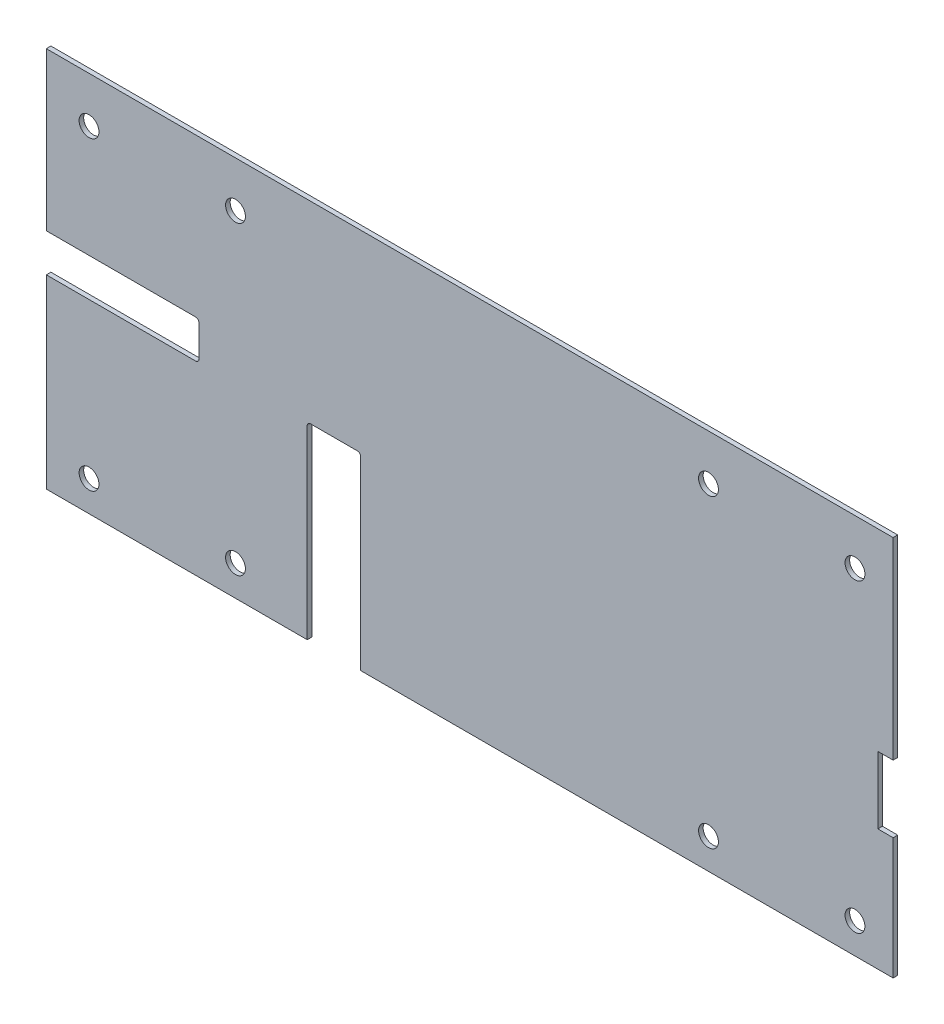
SolidWorks part; units mm, degrees
ref_plane "Plan de face" through (0, 0, 0) normal (0, 0, 1) x (1, 0, 0)
ref_plane "Plan de dessus" through (0, 0, 0) normal (0, 1, 0) x (1, 0, 0)
ref_plane "Plan de droite" through (0, 0, 0) normal (1, 0, 0) x (0, 0, -1)
sketch "Esquisse1" plane through (0, 0, 0) normal (0, 0, 1) x (1, 0, 0)
  line L1 (277.5, -125) -> (-277.5, -125)
  line L2 (277.5, -125) -> (277.5, 125)
  line L3 (277.5, 125) -> (-277.5, 125)
  line L4 (-277.5, -125) -> (-277.5, 125)
  line L5 (277.5, -125) -> (-277.5, 125) construction
  line L6 (277.5, 125) -> (-277.5, -125) construction
  line L7 (-249.5, 95) -> (-153.5, 95) construction
  line L8 (-249.5, 95) -> (-249.5, -105) construction
  line L9 (-249.5, -105) -> (-153.5, -105) construction
  line L10 (-153.5, 95) -> (-153.5, -105) construction
  line L11 (156.5, 95) -> (252.5, 95) construction
  line L12 (156.5, 95) -> (156.5, -105) construction
  line L13 (156.5, -105) -> (252.5, -105) construction
  line L14 (252.5, 95) -> (252.5, -105) construction
  circle A0 centre (156.5, 95) radius 6.5
  circle A1 centre (252.5, 95) radius 6.5
  circle A2 centre (156.5, -105) radius 6.5
  circle A3 centre (252.5, -105) radius 6.5
  circle A4 centre (-153.5, -105) radius 6.5
  circle A5 centre (-153.5, 95) radius 6.5
  circle A6 centre (-249.5, 95) radius 6.5
  circle A7 centre (-249.5, -105) radius 6.5
  point P0 (0, 0)
  dimension "D11" = 13
  dimension "D1" = 555
  dimension "D2" = 250
  dimension "D3" = 96
  dimension "D4" = 96
  dimension "D5" = 200
  dimension "D6" = 20
  dimension "D7" = 0
  dimension "D8" = 502
  dimension "D9" = 25
  dimension "D10" = 0
extrude "Boss.-Extru.1" add sketch "Esquisse1" along normal blind 3
sketch "Esquisse2" plane through (0, 0, 3) normal (0, 0, 1) x (1, 0, 0)
  line L0 (277.5, 125) -> (-277.5, 125) construction
  line L1 (-277.5, 125) -> (-177.5, 125)
  line L2 (-277.5, 125) -> (-277.5, 122)
  line L3 (-277.5, 122) -> (-177.5, 122)
  line L4 (-177.5, 125) -> (-177.5, 122)
  line L5 (-100, 125) -> (100, 125)
  line L6 (-100, 125) -> (-100, 122)
  line L7 (-100, 122) -> (100, 122)
  line L8 (100, 125) -> (100, 122)
  line L9 (277.5, -125) -> (277.5, 125) construction
  line L10 (277.5, 125) -> (177.545, 125)
  line L12 (274.5, 122) -> (177.545, 122)
  line L13 (177.545, 125) -> (177.545, 122)
  line L14 (277.5, -125) -> (274.5, -125)
  line L15 (277.5, -125) -> (277.5, -50)
  line L16 (277.5, -50) -> (274.5, -50)
  line L17 (274.5, -125) -> (274.5, -50)
  line L18 (277.5, 40) -> (274.5, 40)
  line L19 (277.5, 40) -> (277.5, 125)
  line L21 (274.5, 40) -> (274.5, 122)
  point P16 (0, 122)
  dimension "D1" = 100
  dimension "D2" = 100
  dimension "D3" = 3
  dimension "D4" = 0
  dimension "D5" = 200
  dimension "D6" = 3
  dimension "D7" = 75
  dimension "D8" = 85
extrude "Enlèv. mat.-Extru.1" [suppressed] cut sketch "Esquisse2" against normal blind 10
sketch "Esquisse3" [suppressed] plane through (0, 0, 3) normal (0, 0, 1) x (1, 0, 0)
  line L0 (274.5, 122) -> (274.5, 40) construction
  line L1 (-75.5, 122) -> (-72.5, 122)
  line L2 (-75.5, 122) -> (-75.5, 40)
  line L3 (-75.5, 40) -> (-72.5, 40)
  line L4 (-72.5, 122) -> (-72.5, 40)
  line L5 (-100, 122) -> (100, 122) construction
  line L7 (-277.5, -125) -> (274.5, -125) construction
  line L8 (-75.5, -125) -> (-72.5, -125)
  line L9 (-75.5, -125) -> (-75.5, -50)
  line L10 (-75.5, -50) -> (-72.5, -50)
  line L11 (-72.5, -125) -> (-72.5, -50)
  dimension "D1" = 3
  dimension "D2" = 350
  dimension "D3" = 0
  dimension "D4" = 82
  dimension "D5" = 75
  dimension "D6" = 0
extrude "Enlèv. mat.-Extru.2" [suppressed] cut sketch "Esquisse3" against normal blind 3
mirror "Symétrie1" [suppressed] about plane through (0, 0, 0) normal (1, 0, 0)
sketch "Esquisse4" plane through (0, 0, 3) normal (0, 0, 1) x (1, 0, 0)
  line L0 (-277.5, 125) -> (-277.5, -125) construction
  line L1 (-277.5, -3.371) -> (-177.5, -3.371)
  line L2 (-277.5, -3.371) -> (-277.5, 21.629)
  line L3 (-277.5, 21.629) -> (-177.5, 21.629)
  line L4 (-177.5, -3.371) -> (-177.5, 21.629)
  line L6 (-71.5, -1.371) -> (-106.5, -1.371)
  line L7 (-71.5, -1.371) -> (-71.5, -125)
  line L8 (-71.5, -125) -> (-106.5, -125)
  line L9 (-106.5, -1.371) -> (-106.5, -125)
  line L11 (-277.5, -125) -> (277.5, -125) construction
  line L12 (-277.5, 125) -> (-277.5, -125) construction
  line L13 (-274.5, -3.371) -> (-277.5, -3.371) construction
  line L14 (277.5, -125) -> (277.5, 125) construction
  line L15 (277.5, -1.371) -> (267.5, -1.371)
  line L16 (277.5, -1.371) -> (277.5, -45.371)
  line L17 (277.5, -45.371) -> (267.5, -45.371)
  line L18 (267.5, -1.371) -> (267.5, -45.371)
  dimension "D1" = 35
  dimension "D2" = 171
  dimension "D3" = 0
  dimension "D4" = 25
  dimension "D5" = 100
  dimension "D6" = 2
  dimension "D7" = 10
  dimension "D8" = 44
extrude "Enlèv. mat.-Extru.3" cut sketch "Esquisse4" against normal blind 10
sketch "Esquisse6" [suppressed] plane through (0, 0, 3) normal (0, 0, 1) x (1, 0, 0)
  line L1 (-274.5, -50) -> (-277.5, -50)
  line L2 (-274.5, -50) -> (-274.5, -45)
  line L3 (-274.5, -45) -> (-277.5, -45)
  line L4 (-277.5, -50) -> (-277.5, -45)
extrude "Enlèv. mat.-Extru.4" [suppressed] cut sketch "Esquisse6" against normal blind 10
fillet "Congé1" radius 2 4 edges at (-71.5, -1.371, 1.5) (-106.5, -1.371, 1.5) (-177.5, -3.371, 1.5) (-177.5, 21.629, 1.5)
